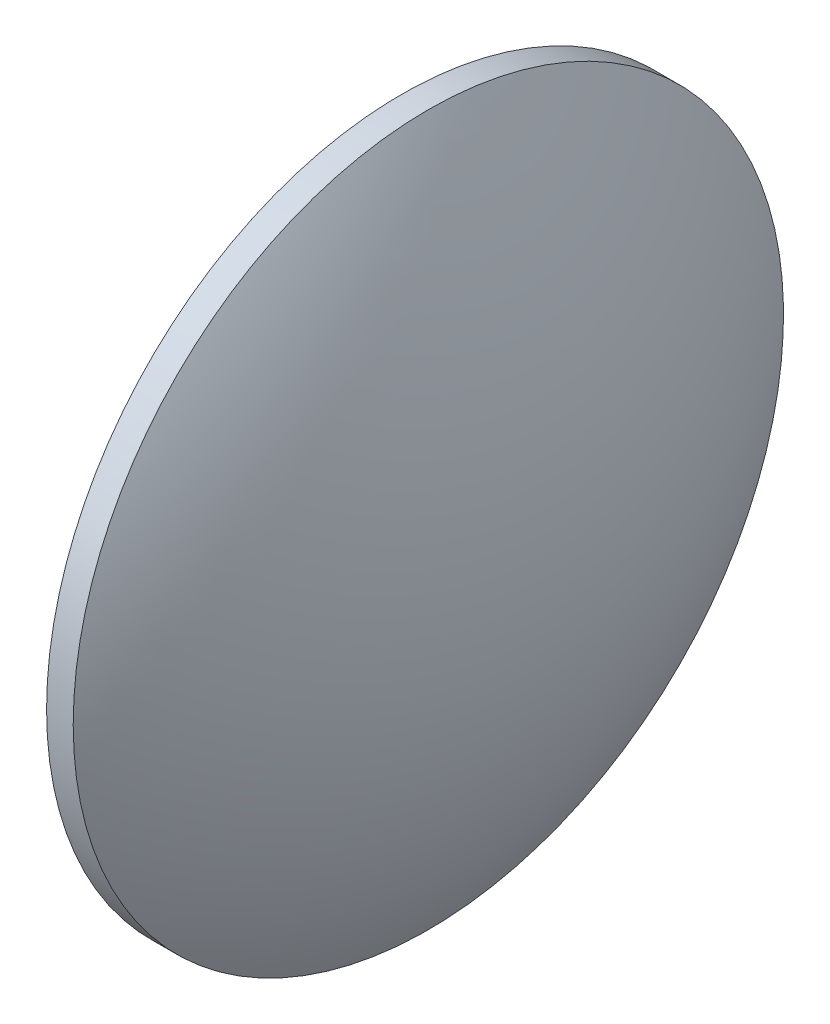
SolidWorks part; units mm, degrees
ref_plane "前视基准面" through (0, 0, 0) normal (0, 0, 1) x (1, 0, 0)
ref_plane "上视基准面" through (0, 0, 0) normal (0, 1, 0) x (1, 0, 0)
ref_plane "右视基准面" through (0, 0, 0) normal (1, 0, 0) x (0, 0, -1)
sketch "草图1" plane through (0, 0, 0) normal (0, 0, 1) x (1, 0, 0)
  line L0 (217.3311, 130.0419) -> (271.1141, 130.0419) construction
  line L1 (236.1561, 130.0419) -> (236.1561, 170.0419)
  line L2 (250.2761, 130.0419) -> (236.1561, 130.0419)
  line L5 (239.1561, 170.0419) -> (236.1561, 170.0419)
  arc A0 (250.2761, 130.0419) -> (239.1561, 170.0419) centre (172.7737, 130.0419) ccw
revolve "旋转1" add sketch "草图1" angle 360 about L0
